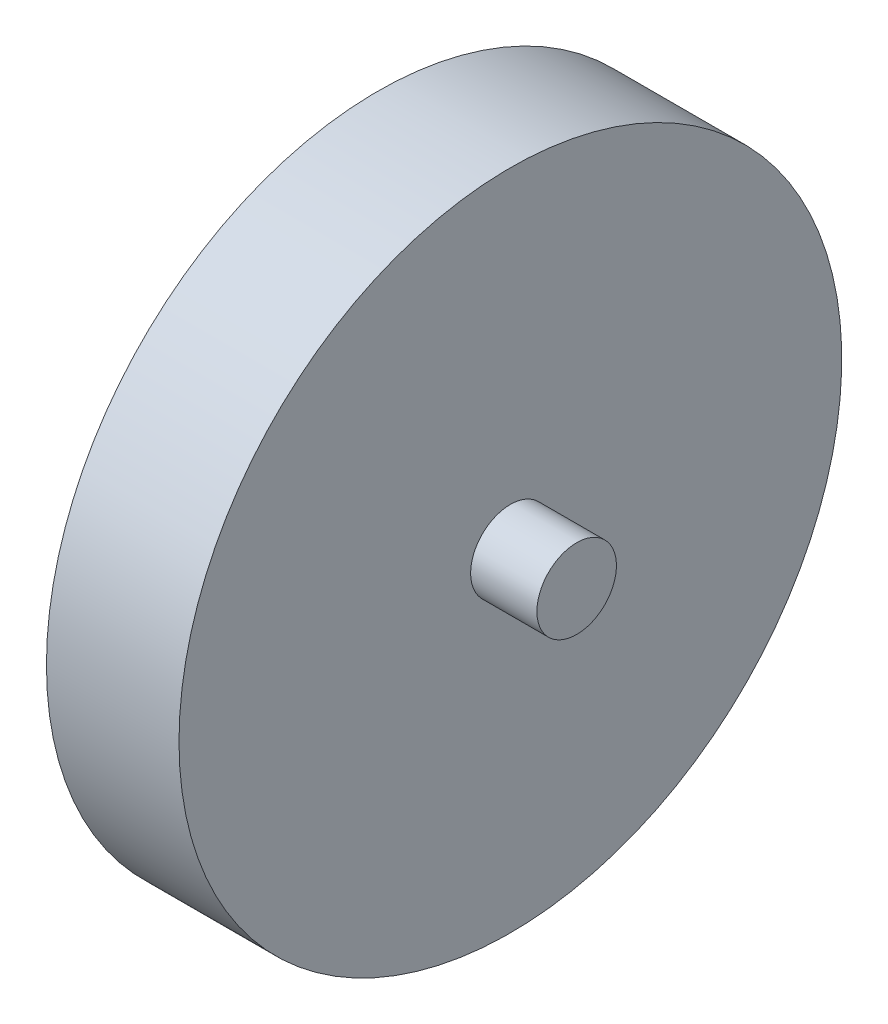
SolidWorks part; units mm, degrees
ref_plane "Plano frontal" through (0, 0, 0) normal (0, 0, 1) x (1, 0, 0)
ref_plane "Plano superior" through (0, 0, 0) normal (0, 1, 0) x (1, 0, 0)
ref_plane "Plano direito" through (0, 0, 0) normal (1, 0, 0) x (0, 0, -1)
sketch "Esboço1" plane through (0, 0, 0) normal (0, 0, 1) x (1, 0, 0)
  line L0 (0, 0) -> (0, 50)
  line L1 (0, 50) -> (20, 50)
  line L2 (20, 50) -> (20, 6)
  line L3 (20, 6) -> (30, 6)
  line L4 (30, 6) -> (30, 0)
  line L5 (30, 0) -> (0, 0)
  line L6 (0, 0) -> (138.9824, 0) construction
  dimension "D1" = 12
  dimension "D2" = 10
  dimension "D3" = 20
  dimension "D4" = 100
revolve "Revolução1" add sketch "Esboço1" angle 360 about L6
